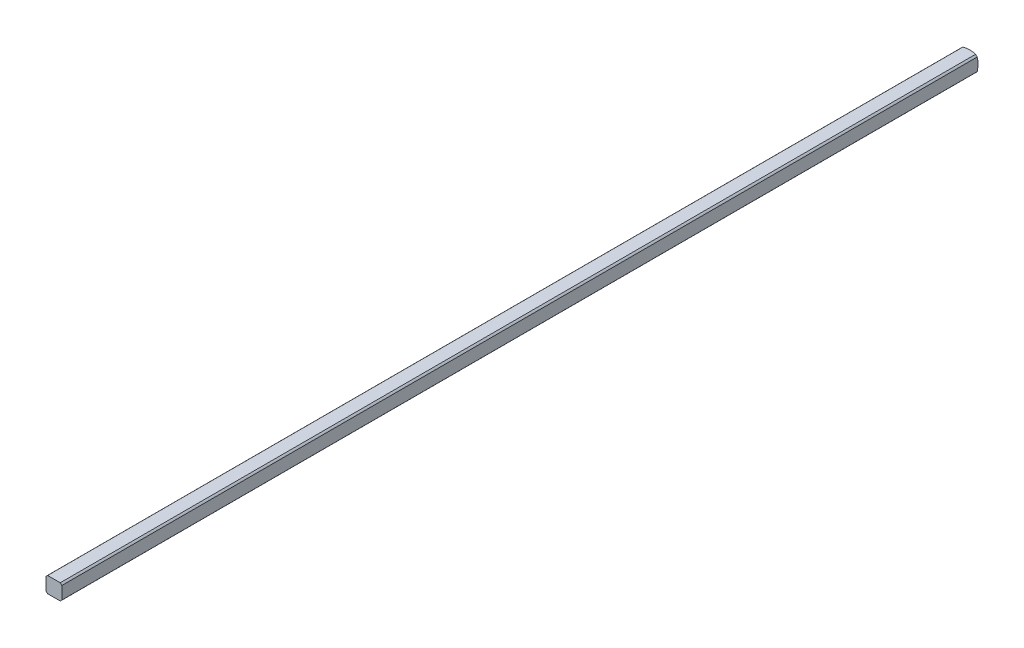
SolidWorks part; units mm, degrees
material "Custom Plastic"
ref_plane "Front Plane" through (0, 0, 0) normal (0, 0, 1) x (1, 0, 0)
ref_plane "Top Plane" through (0, 0, 0) normal (0, 1, 0) x (1, 0, 0)
ref_plane "Right Plane" through (0, 0, 0) normal (1, 0, 0) x (0, 0, -1)
sketch "Sketch1" plane through (0, 0, 0) normal (0, 0, 1) x (1, 0, 0)
  line L0 (-1.5875, -1.5875) -> (1.5875, 1.5875) construction
  line L1 (-1.5875, -1.5875) -> (1.5875, -1.5875)
  line L2 (-1.5875, -1.5875) -> (-1.5875, 1.5875)
  line L3 (-1.5875, 1.5875) -> (1.5875, 1.5875)
  line L4 (1.5875, -1.5875) -> (1.5875, 1.5875)
  dimension "D1" = 3.175
extrude "Boss-Extrude1" add sketch "Sketch1" along normal blind 152.4
sketch "Sketch2" plane through (0, 0, 0) normal (0, 0, -1) x (-1, 0, 0)
  circle A0 centre (0, 0) radius 2.032
  dimension "D1" = 4.064
extrude "Cut-Extrude1" cut sketch "Sketch2" against normal through all flip side to cut
ref_axis "Axis1" through (0, 0, 152.4) along (0, 0, -1)
sketch "Sketch3" plane through (0, 0, 0) normal (0, 1, 0) x (1, 0, 0)
  line L1 (-5.0537, -4.4027) -> (-5.0537, 5.7405)
  line L2 (-5.0537, 5.7405) -> (0, 5.7405)
  line L5 (0, -152.4) -> (0, 0) construction
  line L8 (0, 0.1609) -> (0, 5.7405)
  arc A0 (-5.0537, -4.4027) -> (0, 0.1609) centre (0, -4.9191) cw
  dimension "D1" = 5.08
revolve "Cut-Revolve1" cut sketch "Sketch3" angle 360 about axis through (0, 0, 152.4) along (0, 0, -1)
mirror "Mirror1" about plane through (0, 0, 152.4) normal (0, 0, -1) of bodies 103
sketch "Sketch4" plane through (1.5875, 0, 0) normal (1, 0, 0) x (0, 0, -1)
  line L0 (-304.5368, -1.5875) -> (-304.5368, 1.5875)
  line L1 (-304.5368, -1.5875) -> (-183.8868, -1.5875)
  line L2 (-304.5368, 1.5875) -> (-183.8868, 1.5875)
  line L3 (-183.8868, -1.5875) -> (-183.8868, 1.5875)
  dimension "D1" = 120.65
extrude "Cut-Extrude2" cut sketch "Sketch4" against normal through all
